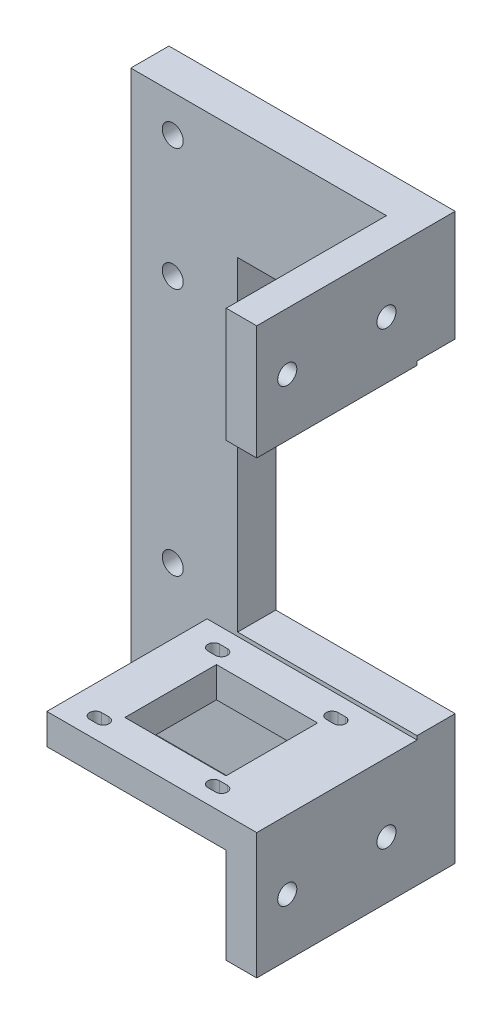
SolidWorks part; units mm, degrees
ref_plane "Plan de face" through (0, 0, 0) normal (0, 0, 1) x (1, 0, 0)
ref_plane "Plan de dessus" through (0, 0, 0) normal (0, 1, 0) x (1, 0, 0)
ref_plane "Plan de droite" through (0, 0, 0) normal (1, 0, 0) x (0, 0, -1)
sketch "Sketch1" plane through (0, 0, 0) normal (0, 0, 1) x (1, 0, 0)
  line L1 (-10, -144) -> (65, -144)
  line L2 (-10, -144) -> (-10, 4)
  line L3 (-10, 4) -> (65, 4)
  line L4 (65, -144) -> (65, 4)
  dimension "D1" = 148
  dimension "D3" = 75
  dimension "D4" = 65
extrude "Boss-Extrude1" add sketch "Sketch1" along normal blind 10
sketch "Sketch2" plane through (0, 0, 10) normal (0, 0, 1) x (1, 0, 0)
  line L1 (10, -111) -> (65, -111)
  line L2 (10, -111) -> (10, -119)
  line L3 (10, -119) -> (65, -119)
  line L4 (65, -111) -> (65, -119)
  line L5 (-10, -144) -> (65, -144) construction
  line L6 (65, -144) -> (65, 4) construction
  dimension "D1" = 25
  dimension "D2" = 8
  dimension "D3" = 55
extrude "Boss-Extrude2" add sketch "Sketch2" along normal blind 42
sketch "Sketch3" plane through (0, -119, 0) normal (0, -1, 0) x (-1, 0, 0)
  line L2 (-10, -52) -> (-65, -52) construction
  line L3 (-21.6, -19.15) -> (-48.1, -19.15)
  line L4 (-21.6, -19.15) -> (-21.6, -43.15)
  line L5 (-21.6, -43.15) -> (-48.1, -43.15)
  line L6 (-48.1, -19.15) -> (-48.1, -43.15)
  line L7 (-21.6, -19.15) -> (-48.1, -43.15) construction
  line L8 (-21.6, -43.15) -> (-48.1, -19.15) construction
  line L9 (-10, -52) -> (-10, -10) construction
  point P0 (-34.85, -31.15)
  dimension "D1" = 20.85
  dimension "D2" = 24.85
  dimension "D3" = 26.5
  dimension "D4" = 24
extrude "Cut-Extrude1" cut sketch "Sketch3" against normal up to surface (8 mm away) up to face at (44.375, -111, 36.25)
sketch "Sketch4" plane through (0, 0, 10) normal (0, 0, 1) x (1, 0, 0)
  line L0 (10, -119) -> (65, -119) construction
  line L1 (65, 4) -> (57, 4)
  line L2 (65, 4) -> (65, -26)
  line L3 (65, -26) -> (57, -26)
  line L4 (57, 4) -> (57, -26)
  line L5 (65, -144) -> (57, -144)
  line L7 (65, -144) -> (65, -119)
  line L8 (65, -119) -> (57, -119)
  line L9 (57, -144) -> (57, -119)
  dimension "D1" = 8
  dimension "D2" = 30
  dimension "D3" = 8
extrude "Boss-Extrude3" add sketch "Sketch4" along normal blind 42
sketch "Sketch5" plane through (57, 0, 0) normal (-1, 0, 0) x (0, 0, 1)
  line L0 (10, 4) -> (10, -26) construction
  line L1 (52, 4) -> (52, -26) construction
  line L2 (52, 4) -> (10, 4) construction
  line L3 (0, -70) -> (10, -70) construction
  line L4 (0, 4) -> (0, -144) construction
  line L5 (10, 4) -> (10, -144) construction
  circle A0 centre (18, -11) radius 2.5
  circle A1 centre (44, -11) radius 2.5
  circle A2 centre (44, -129) radius 2.5
  circle A3 centre (18, -129) radius 2.5
  dimension "D1" = 5
  dimension "D2" = 5
  dimension "D3" = 8
  dimension "D4" = 8
  dimension "D5" = 15
  dimension "D6" = 15
extrude "Cut-Extrude2" cut sketch "Sketch5" against normal up to surface (8 mm away) up to face at (65, -74.5625, 31.125)
sketch "Sketch6" plane through (0, -119, 0) normal (0, -1, 0) x (-1, 0, 0)
  line L0 (-10, -52) -> (-57, -52) construction
  line L1 (-19.4, -46.65) -> (-50.4, -46.65) construction
  line L2 (-19.4, -46.65) -> (-19.4, -15.65) construction
  line L3 (-19.4, -15.65) -> (-50.4, -15.65) construction
  line L4 (-50.4, -46.65) -> (-50.4, -15.65) construction
  line L5 (-10, -52) -> (-10, -10) construction
  line L7 (-19.4, -46.65) -> (-17.4, -46.65) construction
  line L8 (-19.4, -45.1) -> (-17.4, -45.1)
  line L9 (-19.4, -48.2) -> (-17.4, -48.2)
  line L10 (-19.4, -15.65) -> (-17.4, -15.65) construction
  line L11 (-19.4, -14.1) -> (-17.4, -14.1)
  line L12 (-19.4, -17.2) -> (-17.4, -17.2)
  line L13 (-50.4, -46.65) -> (-48.4, -46.65) construction
  line L14 (-50.4, -45.1) -> (-48.4, -45.1)
  line L15 (-50.4, -48.2) -> (-48.4, -48.2)
  line L16 (-50.4, -15.65) -> (-48.4, -15.65) construction
  line L17 (-50.4, -14.1) -> (-48.4, -14.1)
  line L18 (-50.4, -17.2) -> (-48.4, -17.2)
  arc A0 (-19.4, -45.1) -> (-19.4, -48.2) centre (-19.4, -46.65) ccw
  arc A1 (-17.4, -48.2) -> (-17.4, -45.1) centre (-17.4, -46.65) ccw
  arc A2 (-19.4, -14.1) -> (-19.4, -17.2) centre (-19.4, -15.65) ccw
  arc A3 (-17.4, -17.2) -> (-17.4, -14.1) centre (-17.4, -15.65) ccw
  arc A4 (-50.4, -45.1) -> (-50.4, -48.2) centre (-50.4, -46.65) ccw
  arc A5 (-48.4, -48.2) -> (-48.4, -45.1) centre (-48.4, -46.65) ccw
  arc A6 (-50.4, -14.1) -> (-50.4, -17.2) centre (-50.4, -15.65) ccw
  arc A7 (-48.4, -17.2) -> (-48.4, -14.1) centre (-48.4, -15.65) ccw
  point P11 (-18.4, -15.65)
  point P13 (-18.4, -46.65)
  point P24 (-49.4, -46.65)
  point P31 (-49.4, -15.65)
  dimension "D1" = 31
  dimension "D2" = 31
  dimension "D9" = 1.55
  dimension "D10" = 1.55
  dimension "D5" = 1.55
  dimension "D8" = 1
  dimension "D14" = 1.55
  dimension "D3" = 5.35
  dimension "D4" = 9.4
  dimension "D6" = 2
  dimension "D7" = 1
  dimension "D11" = 2
  dimension "D12" = 2
  dimension "D13" = 1
  dimension "D15" = 2
  dimension "D16" = 1
extrude "Cut-Extrude3" cut sketch "Sketch6" against normal up to surface (8 mm away) up to face at (34.85, -111, 31.15)
sketch "Sketch10" plane through (0, 0, 0) normal (0, 0, -1) x (-1, 0, 0)
  line L0 (10, 4) -> (10, -144) construction
  line L1 (-65, 4) -> (10, 4) construction
  circle A0 centre (-1, -102.8) radius 2.75
  circle A1 centre (-1, -134.8) radius 2.75
  circle A2 centre (-1, -37.7) radius 2.75
  circle A3 centre (-1, -5.7) radius 2.75
  dimension "D1" = 5.5
  dimension "D2" = 5.5
  dimension "D3" = 5.5
  dimension "D4" = 5.5
  dimension "D5" = 11
  dimension "D6" = 32
  dimension "D7" = 65.1
  dimension "D8" = 32
  dimension "D9" = 9.7
extrude "Cut-Extrude5" cut sketch "Sketch10" against normal up to surface (10 mm away) up to face at (36.2, -83.45, 10)
sketch "Sketch11" plane through (0, 0, 0) normal (0, 0, -1) x (-1, 0, 0)
  line L0 (-65, -144) -> (-65, 4) construction
  line L1 (-65, -25) -> (-18, -25)
  line L2 (-65, -25) -> (-65, -110)
  line L3 (-65, -110) -> (-18, -110)
  line L4 (-18, -25) -> (-18, -110)
  line L5 (-65, -111) -> (-65, -26) construction
  line L6 (10, -144) -> (-65, -144) construction
  dimension "D1" = 47
  dimension "D2" = 85
  dimension "D3" = 34
extrude "Cut-Extrude6" cut sketch "Sketch11" against normal blind 10
